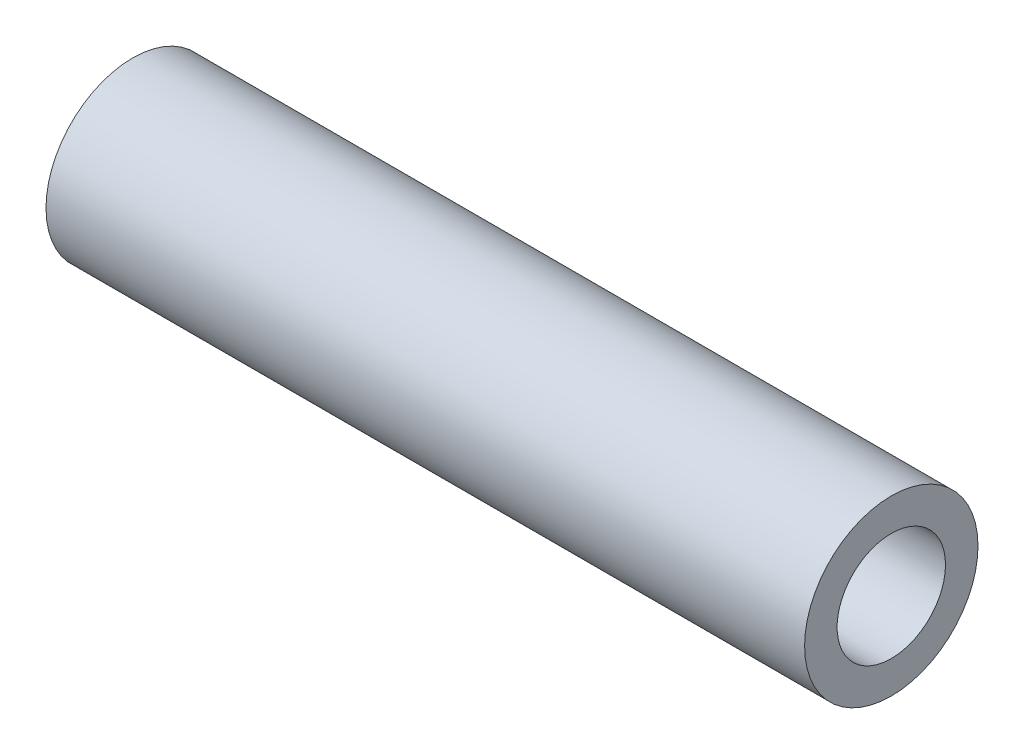
SolidWorks part; units mm, degrees
ref_plane "Front Plane" through (0, 0, 0) normal (0, 0, 1) x (1, 0, 0)
ref_plane "Top Plane" through (0, 0, 0) normal (0, 1, 0) x (1, 0, 0)
ref_plane "Right Plane" through (0, 0, 0) normal (1, 0, 0) x (0, 0, -1)
sketch "Sketch1" plane through (0, 0, 0) normal (1, 0, 0) x (0, 0, -1)
  circle A0 centre (0, 0) radius 5
  circle A1 centre (0, 0) radius 8
  dimension "D1" = 10
  dimension "D2" = 16
extrude "Boss-Extrude1" add sketch "Sketch1" along normal blind 70
